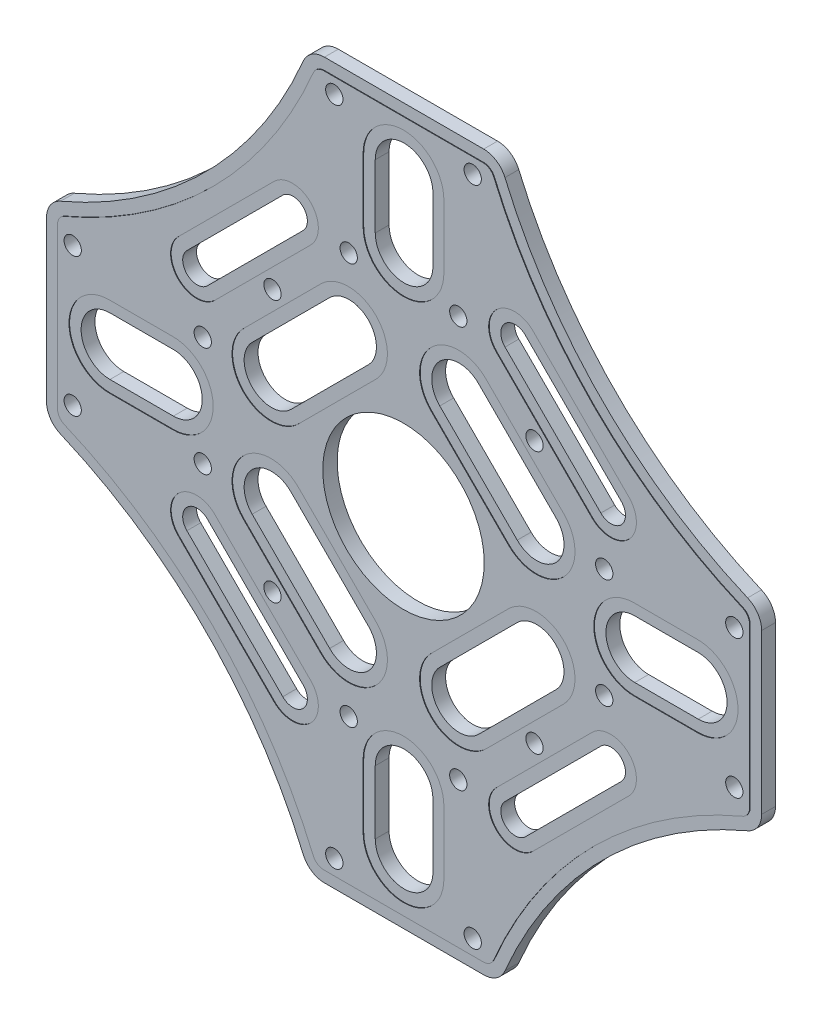
SolidWorks part; units mm, degrees
ref_plane "Alzado" through (0, 0, 0) normal (0, 0, 1) x (1, 0, 0)
ref_plane "Planta" through (0, 0, 0) normal (0, 1, 0) x (1, 0, 0)
ref_plane "Vista lateral" through (0, 0, 0) normal (1, 0, 0) x (0, 0, -1)
sketch "Croquis1" plane through (0, 0, 0) normal (0, 0, 1) x (1, 0, 0)
  line L0 (0, 62) -> (0, -62) construction
  line L1 (16.5, -62) -> (-16.5, -62)
  line L2 (16.5, -62) -> (16.5, -9.3094) construction
  line L3 (16.5, 62) -> (-16.5, 62)
  line L4 (-16.5, -62) -> (-16.5, -9.3094) construction
  line L5 (-62, 0) -> (62, 0) construction
  line L6 (0, 51) -> (0, 40) construction
  line L7 (62, -16.5) -> (9.3094, -16.5) construction
  line L8 (62, -16.5) -> (62, 16.5)
  line L9 (62, 16.5) -> (0, 16.5) construction
  line L10 (-62, -16.5) -> (-62, 16.5)
  line L11 (5, 51) -> (5, 40)
  line L12 (-5, 51) -> (-5, 40)
  line L13 (51, 0) -> (40, 0) construction
  line L14 (51, -5) -> (40, -5)
  line L15 (51, 5) -> (40, 5)
  line L16 (0, -51) -> (0, -40) construction
  line L17 (-5, -51) -> (-5, -40)
  line L18 (5, -51) -> (5, -40)
  line L19 (-51, 0) -> (-40, 0) construction
  line L20 (-51, 5) -> (-40, 5)
  line L21 (-51, -5) -> (-40, -5)
  line L22 (0, 0) -> (9.8995, -9.8995) construction
  line L23 (-35.8857, -19.2687) -> (-19.2687, -35.8857) construction
  line L24 (-34.1179, -17.5009) -> (-17.5009, -34.1179)
  line L25 (-37.6534, -21.0364) -> (-21.0364, -37.6534)
  line L26 (-22.981, -9.5459) -> (-9.5459, -22.981) construction
  line L27 (-19.6222, -6.1872) -> (-6.1872, -19.6222)
  line L28 (-26.3397, -12.9047) -> (-12.9047, -26.3397)
  line L29 (19.2687, -35.8857) -> (35.8857, -19.2687) construction
  line L30 (17.5009, -34.1179) -> (34.1179, -17.5009)
  line L31 (21.0364, -37.6534) -> (37.6534, -21.0364)
  line L32 (9.5459, -22.981) -> (22.981, -9.5459) construction
  line L33 (6.1872, -19.6222) -> (19.6222, -6.1872)
  line L34 (12.9047, -26.3397) -> (26.3397, -12.9047)
  line L35 (-19.2687, 35.8857) -> (-35.8857, 19.2687) construction
  line L36 (-17.5009, 34.1179) -> (-34.1179, 17.5009)
  line L37 (-21.0364, 37.6534) -> (-37.6534, 21.0364)
  line L38 (-9.5459, 22.981) -> (-22.981, 9.5459) construction
  line L39 (-6.1872, 19.6222) -> (-19.6222, 6.1872)
  line L40 (-12.9047, 26.3397) -> (-26.3397, 12.9047)
  line L41 (35.8857, 19.2687) -> (19.2687, 35.8857) construction
  line L42 (34.1179, 17.5009) -> (17.5009, 34.1179)
  line L43 (37.6534, 21.0364) -> (21.0364, 37.6534)
  line L44 (22.981, 9.5459) -> (9.5459, 22.981) construction
  line L45 (19.6222, 6.1872) -> (6.1872, 19.6222)
  line L46 (26.3397, 12.9047) -> (12.9047, 26.3397)
  line L47 (-9.3094, 16.5) -> (-62, 16.5) construction
  line L48 (-16.5, 9.3094) -> (-16.5, 62) construction
  line L49 (-9.3094, -16.5) -> (-62, -16.5) construction
  line L50 (16.5, 0) -> (16.5, 62) construction
  line L51 (12.9047, -12.9047) -> (56.3792, -56.3792) construction
  line L52 (29.3449, -29.3449) -> (34.2947, -34.2947)
  circle A0 centre (0, 0) radius 14
  arc A1 (5, 51) -> (-5, 51) centre (0, 51) ccw
  arc A2 (-5, 40) -> (5, 40) centre (0, 40) ccw
  arc A3 (51, -5) -> (51, 5) centre (51, 0) ccw
  arc A4 (40, 5) -> (40, -5) centre (40, 0) ccw
  arc A5 (-5, -51) -> (5, -51) centre (0, -51) ccw
  arc A6 (5, -40) -> (-5, -40) centre (0, -40) ccw
  arc A7 (-51, 5) -> (-51, -5) centre (-51, 0) ccw
  arc A8 (-40, -5) -> (-40, 5) centre (-40, 0) ccw
  arc A9 (-34.1179, -17.5009) -> (-37.6534, -21.0364) centre (-35.8857, -19.2687) ccw
  arc A10 (-21.0364, -37.6534) -> (-17.5009, -34.1179) centre (-19.2687, -35.8857) ccw
  arc A11 (-19.6222, -6.1872) -> (-26.3397, -12.9047) centre (-22.981, -9.5459) ccw
  arc A12 (-12.9047, -26.3397) -> (-6.1872, -19.6222) centre (-9.5459, -22.981) ccw
  arc A13 (17.5009, -34.1179) -> (21.0364, -37.6534) centre (19.2687, -35.8857) ccw
  arc A14 (37.6534, -21.0364) -> (34.1179, -17.5009) centre (35.8857, -19.2687) ccw
  arc A15 (6.1872, -19.6222) -> (12.9047, -26.3397) centre (9.5459, -22.981) ccw
  arc A16 (26.3397, -12.9047) -> (19.6222, -6.1872) centre (22.981, -9.5459) ccw
  arc A17 (-17.5009, 34.1179) -> (-21.0364, 37.6534) centre (-19.2687, 35.8857) ccw
  arc A18 (-37.6534, 21.0364) -> (-34.1179, 17.5009) centre (-35.8857, 19.2687) ccw
  arc A19 (-6.1872, 19.6222) -> (-12.9047, 26.3397) centre (-9.5459, 22.981) ccw
  arc A20 (-26.3397, 12.9047) -> (-19.6222, 6.1872) centre (-22.981, 9.5459) ccw
  arc A21 (34.1179, 17.5009) -> (37.6534, 21.0364) centre (35.8857, 19.2687) ccw
  arc A22 (21.0364, 37.6534) -> (17.5009, 34.1179) centre (19.2687, 35.8857) ccw
  arc A23 (19.6222, 6.1872) -> (26.3397, 12.9047) centre (22.981, 9.5459) ccw
  arc A24 (12.9047, 26.3397) -> (6.1872, 19.6222) centre (9.5459, 22.981) ccw
  arc A25 (62, -16.5) -> (16.5, -62) centre (90.5636, -90.5636) ccw
  arc A26 (-16.5, -62) -> (-62, -16.5) centre (-90.5636, -90.5636) ccw
  arc A27 (-62, 16.5) -> (-16.5, 62) centre (-90.5636, 90.5636) ccw
  arc A28 (16.5, 62) -> (62, 16.5) centre (90.5636, 90.5636) ccw
  point P0 (0, 0)
  point P6 (0, 0)
  point P18 (0, 45.5)
  point P24 (0, 35)
  point P30 (45.5, 0)
  point P37 (0, -45.5)
  point P44 (-45.5, 0)
  point P49 (0, 0)
  point P53 (-27.5772, -27.5772)
  point P60 (-16.2635, -16.2635)
  point P64 (27.5772, -27.5772)
  point P71 (16.2635, -16.2635)
  point P81 (-27.5772, 27.5772)
  point P88 (-16.2635, 16.2635)
  point P95 (27.5772, 27.5772)
  point P102 (16.2635, 16.2635)
  point P107 (0, 0)
  point P130 (0, 0)
  dimension "D5" = 28
  dimension "D9" = 4
  dimension "D1" = 124
  dimension "D2" = 33
  dimension "D3" = 124
  dimension "D4" = 33
  dimension "D6" = 10.5
  dimension "D7" = 10
  dimension "D8" = 45.5
  dimension "D10" = 45
  dimension "D11" = 23
  dimension "D12" = 9.5
  dimension "D13" = 5
  dimension "D14" = 39
  dimension "D16" = 7
  dimension "D15" = 4
  dimension "D17" = 4
extrude "Saliente-Extruir1" add sketch "Croquis1" along normal mid plane 2.5
fillet "Redondeo1" radius 4 8 edges at (-62, 16.5, 0) (-62, -16.5, 0) (-16.5, -62, 0) (16.5, -62, 0) (62, -16.5, 0) (62, 16.5, 0) (-16.5, 62, 0) (16.5, 62, 0)
sketch "Croquis2" plane through (0, 0, 1.25) normal (0, 0, 1) x (1, 0, 0)
  line L0 (19.6222, 6.1872) -> (6.1872, 19.6222) construction
  line L1 (26.3397, 12.9047) -> (12.9047, 26.3397) construction
  line L2 (37.6534, 21.0364) -> (21.0364, 37.6534) construction
  line L3 (34.1179, 17.5009) -> (17.5009, 34.1179) construction
  line L4 (19.6222, 6.1872) -> (6.1872, 19.6222)
  line L5 (26.3397, 12.9047) -> (12.9047, 26.3397)
  line L6 (37.6534, 21.0364) -> (21.0364, 37.6534)
  line L7 (34.1179, 17.5009) -> (17.5009, 34.1179)
  line L8 (39.0676, 22.4506) -> (22.4506, 39.0676)
  line L9 (32.7037, 16.0867) -> (16.0867, 32.7037)
  line L10 (18.208, 4.773) -> (4.773, 18.208)
  line L11 (27.7539, 14.3189) -> (14.3189, 27.7539)
  line L12 (5, 51) -> (5, 40) construction
  line L13 (-5, 51) -> (-5, 40) construction
  line L14 (-6.1872, 19.6222) -> (-19.6222, 6.1872) construction
  line L15 (-12.9047, 26.3397) -> (-26.3397, 12.9047) construction
  line L16 (-17.5009, 34.1179) -> (-34.1179, 17.5009) construction
  line L17 (-21.0364, 37.6534) -> (-37.6534, 21.0364) construction
  line L18 (-51, 5) -> (-40, 5) construction
  line L19 (-51, -5) -> (-40, -5) construction
  line L20 (-19.6222, -6.1872) -> (-6.1872, -19.6222) construction
  line L21 (-26.3397, -12.9047) -> (-12.9047, -26.3397) construction
  line L22 (-34.1179, -17.5009) -> (-17.5009, -34.1179) construction
  line L23 (-37.6534, -21.0364) -> (-21.0364, -37.6534) construction
  line L24 (-5, -51) -> (-5, -40) construction
  line L25 (5, -51) -> (5, -40) construction
  line L26 (6.1872, -19.6222) -> (19.6222, -6.1872) construction
  line L27 (12.9047, -26.3397) -> (26.3397, -12.9047) construction
  line L28 (17.5009, -34.1179) -> (34.1179, -17.5009) construction
  line L29 (21.0364, -37.6534) -> (37.6534, -21.0364) construction
  line L30 (51, 5) -> (40, 5) construction
  line L31 (51, -5) -> (40, -5) construction
  line L32 (5, 51) -> (5, 40)
  line L33 (-5, 51) -> (-5, 40)
  line L34 (-6.1872, 19.6222) -> (-19.6222, 6.1872)
  line L35 (-12.9047, 26.3397) -> (-26.3397, 12.9047)
  line L36 (-17.5009, 34.1179) -> (-34.1179, 17.5009)
  line L37 (-21.0364, 37.6534) -> (-37.6534, 21.0364)
  line L38 (-51, 5) -> (-40, 5)
  line L39 (-51, -5) -> (-40, -5)
  line L40 (-19.6222, -6.1872) -> (-6.1872, -19.6222)
  line L41 (-26.3397, -12.9047) -> (-12.9047, -26.3397)
  line L42 (-34.1179, -17.5009) -> (-17.5009, -34.1179)
  line L43 (-37.6534, -21.0364) -> (-21.0364, -37.6534)
  line L44 (-5, -51) -> (-5, -40)
  line L45 (5, -51) -> (5, -40)
  line L46 (6.1872, -19.6222) -> (19.6222, -6.1872)
  line L47 (12.9047, -26.3397) -> (26.3397, -12.9047)
  line L48 (17.5009, -34.1179) -> (34.1179, -17.5009)
  line L49 (21.0364, -37.6534) -> (37.6534, -21.0364)
  line L50 (51, 5) -> (40, 5)
  line L51 (51, -5) -> (40, -5)
  line L52 (-14.3189, 27.7539) -> (-27.7539, 14.3189)
  line L53 (-4.773, 18.208) -> (-18.208, 4.773)
  line L54 (-16.0867, 32.7037) -> (-32.7037, 16.0867)
  line L55 (-22.4506, 39.0676) -> (-39.0676, 22.4506)
  line L56 (-7, 51) -> (-7, 40)
  line L57 (7, 51) -> (7, 40)
  line L58 (-18.208, -4.773) -> (-4.773, -18.208)
  line L59 (-27.7539, -14.3189) -> (-14.3189, -27.7539)
  line L60 (-51, -7) -> (-40, -7)
  line L61 (-51, 7) -> (-40, 7)
  line L62 (-39.0676, -22.4506) -> (-22.4506, -39.0676)
  line L63 (-32.7037, -16.0867) -> (-16.0867, -32.7037)
  line L64 (-7, -51) -> (-7, -40)
  line L65 (7, -51) -> (7, -40)
  line L66 (14.3189, -27.7539) -> (27.7539, -14.3189)
  line L67 (4.773, -18.208) -> (18.208, -4.773)
  line L68 (16.0867, -32.7037) -> (32.7037, -16.0867)
  line L69 (22.4506, -39.0676) -> (39.0676, -22.4506)
  line L70 (51, -7) -> (40, -7)
  line L71 (51, 7) -> (40, 7)
  arc A0 (12.9047, 26.3397) -> (6.1872, 19.6222) centre (9.5459, 22.981) ccw construction
  arc A1 (19.6222, 6.1872) -> (26.3397, 12.9047) centre (22.981, 9.5459) ccw construction
  arc A2 (21.0364, 37.6534) -> (17.5009, 34.1179) centre (19.2687, 35.8857) ccw construction
  arc A3 (34.1179, 17.5009) -> (37.6534, 21.0364) centre (35.8857, 19.2687) ccw construction
  arc A4 (12.9047, 26.3397) -> (6.1872, 19.6222) centre (9.5459, 22.981) ccw
  arc A5 (19.6222, 6.1872) -> (26.3397, 12.9047) centre (22.981, 9.5459) ccw
  arc A6 (21.0364, 37.6534) -> (17.5009, 34.1179) centre (19.2687, 35.8857) ccw
  arc A7 (34.1179, 17.5009) -> (37.6534, 21.0364) centre (35.8857, 19.2687) ccw
  arc A8 (22.4506, 39.0676) -> (16.0867, 32.7037) centre (19.2687, 35.8857) ccw
  arc A9 (32.7037, 16.0867) -> (39.0676, 22.4506) centre (35.8857, 19.2687) ccw
  arc A10 (14.3189, 27.7539) -> (4.773, 18.208) centre (9.5459, 22.981) ccw
  arc A11 (18.208, 4.773) -> (27.7539, 14.3189) centre (22.981, 9.5459) ccw
  arc A12 (5, 51) -> (-5, 51) centre (0, 51) ccw construction
  arc A13 (-5, 40) -> (5, 40) centre (0, 40) ccw construction
  arc A14 (-26.3397, 12.9047) -> (-19.6222, 6.1872) centre (-22.981, 9.5459) ccw construction
  arc A15 (-6.1872, 19.6222) -> (-12.9047, 26.3397) centre (-9.5459, 22.981) ccw construction
  arc A16 (-17.5009, 34.1179) -> (-21.0364, 37.6534) centre (-19.2687, 35.8857) ccw construction
  arc A17 (-37.6534, 21.0364) -> (-34.1179, 17.5009) centre (-35.8857, 19.2687) ccw construction
  arc A18 (-40, -5) -> (-40, 5) centre (-40, 0) ccw construction
  arc A19 (-51, 5) -> (-51, -5) centre (-51, 0) ccw construction
  arc A20 (-34.1179, -17.5009) -> (-37.6534, -21.0364) centre (-35.8857, -19.2687) ccw construction
  arc A21 (-19.6222, -6.1872) -> (-26.3397, -12.9047) centre (-22.981, -9.5459) ccw construction
  arc A22 (-21.0364, -37.6534) -> (-17.5009, -34.1179) centre (-19.2687, -35.8857) ccw construction
  arc A23 (-12.9047, -26.3397) -> (-6.1872, -19.6222) centre (-9.5459, -22.981) ccw construction
  arc A24 (-5, -51) -> (5, -51) centre (0, -51) ccw construction
  arc A25 (5, -40) -> (-5, -40) centre (0, -40) ccw construction
  arc A26 (6.1872, -19.6222) -> (12.9047, -26.3397) centre (9.5459, -22.981) ccw construction
  arc A27 (26.3397, -12.9047) -> (19.6222, -6.1872) centre (22.981, -9.5459) ccw construction
  arc A28 (17.5009, -34.1179) -> (21.0364, -37.6534) centre (19.2687, -35.8857) ccw construction
  arc A29 (37.6534, -21.0364) -> (34.1179, -17.5009) centre (35.8857, -19.2687) ccw construction
  arc A30 (51, -5) -> (51, 5) centre (51, 0) ccw construction
  arc A31 (40, 5) -> (40, -5) centre (40, 0) ccw construction
  arc A32 (5, 51) -> (-5, 51) centre (0, 51) ccw
  arc A33 (-5, 40) -> (5, 40) centre (0, 40) ccw
  arc A34 (-26.3397, 12.9047) -> (-19.6222, 6.1872) centre (-22.981, 9.5459) ccw
  arc A35 (-6.1872, 19.6222) -> (-12.9047, 26.3397) centre (-9.5459, 22.981) ccw
  arc A36 (-17.5009, 34.1179) -> (-21.0364, 37.6534) centre (-19.2687, 35.8857) ccw
  arc A37 (-37.6534, 21.0364) -> (-34.1179, 17.5009) centre (-35.8857, 19.2687) ccw
  arc A38 (-40, -5) -> (-40, 5) centre (-40, 0) ccw
  arc A39 (-51, 5) -> (-51, -5) centre (-51, 0) ccw
  arc A40 (-34.1179, -17.5009) -> (-37.6534, -21.0364) centre (-35.8857, -19.2687) ccw
  arc A41 (-19.6222, -6.1872) -> (-26.3397, -12.9047) centre (-22.981, -9.5459) ccw
  arc A42 (-21.0364, -37.6534) -> (-17.5009, -34.1179) centre (-19.2687, -35.8857) ccw
  arc A43 (-12.9047, -26.3397) -> (-6.1872, -19.6222) centre (-9.5459, -22.981) ccw
  arc A44 (-5, -51) -> (5, -51) centre (0, -51) ccw
  arc A45 (5, -40) -> (-5, -40) centre (0, -40) ccw
  arc A46 (6.1872, -19.6222) -> (12.9047, -26.3397) centre (9.5459, -22.981) ccw
  arc A47 (26.3397, -12.9047) -> (19.6222, -6.1872) centre (22.981, -9.5459) ccw
  arc A48 (17.5009, -34.1179) -> (21.0364, -37.6534) centre (19.2687, -35.8857) ccw
  arc A49 (37.6534, -21.0364) -> (34.1179, -17.5009) centre (35.8857, -19.2687) ccw
  arc A50 (51, -5) -> (51, 5) centre (51, 0) ccw
  arc A51 (40, 5) -> (40, -5) centre (40, 0) ccw
  arc A52 (-4.773, 18.208) -> (-14.3189, 27.7539) centre (-9.5459, 22.981) ccw
  arc A53 (-27.7539, 14.3189) -> (-18.208, 4.773) centre (-22.981, 9.5459) ccw
  arc A54 (-39.0676, 22.4506) -> (-32.7037, 16.0867) centre (-35.8857, 19.2687) ccw
  arc A55 (-16.0867, 32.7037) -> (-22.4506, 39.0676) centre (-19.2687, 35.8857) ccw
  arc A56 (-7, 40) -> (7, 40) centre (0, 40) ccw
  arc A57 (7, 51) -> (-7, 51) centre (0, 51) ccw
  arc A58 (-14.3189, -27.7539) -> (-4.773, -18.208) centre (-9.5459, -22.981) ccw
  arc A59 (-18.208, -4.773) -> (-27.7539, -14.3189) centre (-22.981, -9.5459) ccw
  arc A60 (-40, -7) -> (-40, 7) centre (-40, 0) ccw
  arc A61 (-51, 7) -> (-51, -7) centre (-51, 0) ccw
  arc A62 (-22.4506, -39.0676) -> (-16.0867, -32.7037) centre (-19.2687, -35.8857) ccw
  arc A63 (-32.7037, -16.0867) -> (-39.0676, -22.4506) centre (-35.8857, -19.2687) ccw
  arc A64 (7, -40) -> (-7, -40) centre (0, -40) ccw
  arc A65 (-7, -51) -> (7, -51) centre (0, -51) ccw
  arc A66 (4.773, -18.208) -> (14.3189, -27.7539) centre (9.5459, -22.981) ccw
  arc A67 (27.7539, -14.3189) -> (18.208, -4.773) centre (22.981, -9.5459) ccw
  arc A68 (39.0676, -22.4506) -> (32.7037, -16.0867) centre (35.8857, -19.2687) ccw
  arc A69 (16.0867, -32.7037) -> (22.4506, -39.0676) centre (19.2687, -35.8857) ccw
  arc A70 (40, 7) -> (40, -7) centre (40, 0) ccw
  arc A71 (51, -7) -> (51, 7) centre (51, 0) ccw
  dimension "D1" = 2
  dimension "D2" = 2
extrude "Cortar-Extruir1" cut sketch "Croquis2" against normal blind 0.1
sketch "Croquis3" plane through (0, 0, 1.25) normal (0, 0, 1) x (1, 0, 0)
  line L0 (13.8045, 62) -> (-13.8045, 62) construction
  line L1 (-62, -13.8045) -> (-62, 13.8045) construction
  line L2 (13.8045, -62) -> (-13.8045, -62) construction
  line L3 (62, -13.8045) -> (62, 13.8045) construction
  line L4 (13.8045, 62) -> (-13.8045, 62)
  line L5 (-62, -13.8045) -> (-62, 13.8045)
  line L6 (13.8045, -62) -> (-13.8045, -62)
  line L7 (62, -13.8045) -> (62, 13.8045)
  line L8 (60, -13.8045) -> (60, 13.8045)
  line L9 (13.8045, -60) -> (-13.8045, -60)
  line L10 (-60, -13.8045) -> (-60, 13.8045)
  line L11 (13.8045, 60) -> (-13.8045, 60)
  arc A0 (-13.8045, 62) -> (-17.4869, 59.5622) centre (-13.8045, 58) ccw construction
  arc A1 (17.4869, 59.5622) -> (13.8045, 62) centre (13.8045, 58) ccw construction
  arc A2 (-59.5622, 17.4869) -> (-17.4869, 59.5622) centre (-90.5636, 90.5636) ccw construction
  arc A3 (-59.5622, 17.4869) -> (-62, 13.8045) centre (-58, 13.8045) ccw construction
  arc A4 (-62, -13.8045) -> (-59.5622, -17.4869) centre (-58, -13.8045) ccw construction
  arc A5 (-17.4869, -59.5622) -> (-59.5622, -17.4869) centre (-90.5636, -90.5636) ccw construction
  arc A6 (-17.4869, -59.5622) -> (-13.8045, -62) centre (-13.8045, -58) ccw construction
  arc A7 (13.8045, -62) -> (17.4869, -59.5622) centre (13.8045, -58) ccw construction
  arc A8 (59.5622, -17.4869) -> (17.4869, -59.5622) centre (90.5636, -90.5636) ccw construction
  arc A9 (59.5622, -17.4869) -> (62, -13.8045) centre (58, -13.8045) ccw construction
  arc A10 (17.4869, 59.5622) -> (59.5622, 17.4869) centre (90.5636, 90.5636) ccw construction
  arc A11 (62, 13.8045) -> (59.5622, 17.4869) centre (58, 13.8045) ccw construction
  arc A12 (-13.8045, 62) -> (-17.4869, 59.5622) centre (-13.8045, 58) ccw
  arc A13 (17.4869, 59.5622) -> (13.8045, 62) centre (13.8045, 58) ccw
  arc A14 (-59.5622, 17.4869) -> (-17.4869, 59.5622) centre (-90.5636, 90.5636) ccw
  arc A15 (-59.5622, 17.4869) -> (-62, 13.8045) centre (-58, 13.8045) ccw
  arc A16 (-62, -13.8045) -> (-59.5622, -17.4869) centre (-58, -13.8045) ccw
  arc A17 (-17.4869, -59.5622) -> (-59.5622, -17.4869) centre (-90.5636, -90.5636) ccw
  arc A18 (-17.4869, -59.5622) -> (-13.8045, -62) centre (-13.8045, -58) ccw
  arc A19 (13.8045, -62) -> (17.4869, -59.5622) centre (13.8045, -58) ccw
  arc A20 (59.5622, -17.4869) -> (17.4869, -59.5622) centre (90.5636, -90.5636) ccw
  arc A21 (59.5622, -17.4869) -> (62, -13.8045) centre (58, -13.8045) ccw
  arc A22 (17.4869, 59.5622) -> (59.5622, 17.4869) centre (90.5636, 90.5636) ccw
  arc A23 (62, 13.8045) -> (59.5622, 17.4869) centre (58, 13.8045) ccw
  arc A24 (15.6457, 58.7811) -> (58.7811, 15.6457) centre (90.5636, 90.5636) ccw
  arc A25 (60, 13.8045) -> (58.7811, 15.6457) centre (58, 13.8045) ccw
  arc A26 (58.7811, -15.6457) -> (60, -13.8045) centre (58, -13.8045) ccw
  arc A27 (58.7811, -15.6457) -> (15.6457, -58.7811) centre (90.5636, -90.5636) ccw
  arc A28 (13.8045, -60) -> (15.6457, -58.7811) centre (13.8045, -58) ccw
  arc A29 (-15.6457, -58.7811) -> (-13.8045, -60) centre (-13.8045, -58) ccw
  arc A30 (-15.6457, -58.7811) -> (-58.7811, -15.6457) centre (-90.5636, -90.5636) ccw
  arc A31 (-60, -13.8045) -> (-58.7811, -15.6457) centre (-58, -13.8045) ccw
  arc A32 (-58.7811, 15.6457) -> (-60, 13.8045) centre (-58, 13.8045) ccw
  arc A33 (-58.7811, 15.6457) -> (-15.6457, 58.7811) centre (-90.5636, 90.5636) ccw
  arc A34 (-13.8045, 60) -> (-15.6457, 58.7811) centre (-13.8045, 58) ccw
  arc A35 (15.6457, 58.7811) -> (13.8045, 60) centre (13.8045, 58) ccw
  dimension "D1" = 2
extrude "Cortar-Extruir2" cut sketch "Croquis3" against normal blind 0.1
sketch "Croquis4" plane through (0, 0, 1.25) normal (0, 0, 1) x (1, 0, 0)
  line L0 (56, 0) -> (35, 0) construction
  line L2 (33.642, -12) -> (57.358, -12) construction
  line L3 (33.642, -12) -> (33.642, 12) construction
  line L4 (33.642, 12) -> (57.358, 12) construction
  line L5 (57.358, -12) -> (57.358, 12) construction
  line L6 (33.642, -12) -> (57.358, 12) construction
  line L7 (33.642, 12) -> (57.358, -12) construction
  line L8 (56.1921, 9.5) -> (34.8079, 9.5) construction
  line L9 (56.1921, 9.5) -> (56.1921, -9.5) construction
  line L10 (56.1921, -9.5) -> (34.8079, -9.5) construction
  line L11 (34.8079, 9.5) -> (34.8079, -9.5) construction
  line L12 (56.1921, 9.5) -> (34.8079, -9.5) construction
  line L13 (56.1921, -9.5) -> (34.8079, 9.5) construction
  arc A0 (51, -5) -> (51, 5) centre (51, 0) ccw construction
  arc A1 (40, 5) -> (40, -5) centre (40, 0) ccw construction
  circle A2 centre (57.358, 12) radius 1.5
  circle A3 centre (57.358, -12) radius 1.5
  circle A4 centre (34.8079, 9.5) radius 1.5
  circle A5 centre (34.8079, -9.5) radius 1.5
  circle A6 centre (12, -57.358) radius 1.5
  circle A7 centre (-12, -57.358) radius 1.5
  circle A8 centre (-9.5, -34.8079) radius 1.5
  circle A9 centre (9.5, -34.8079) radius 1.5
  circle A10 centre (-57.358, -12) radius 1.5
  circle A11 centre (-57.358, 12) radius 1.5
  circle A12 centre (-34.8079, 9.5) radius 1.5
  circle A13 centre (-34.8079, -9.5) radius 1.5
  circle A14 centre (-12, 57.358) radius 1.5
  circle A15 centre (12, 57.358) radius 1.5
  circle A16 centre (9.5, 34.8079) radius 1.5
  circle A17 centre (-9.5, 34.8079) radius 1.5
  point P8 (45.5, 0)
  point P15 (45.5, 0)
  point P49 (0, 0)
  dimension "D2" = 3
  dimension "D3" = 3
  dimension "D5" = 3
  dimension "D6" = 3
  dimension "D1" = 24
  dimension "D4" = 19
  dimension "D7" = 4
extrude "Cortar-Extruir3" cut sketch "Croquis4" against normal blind 10
sketch "Croquis5" plane through (0, 0, 1.25) normal (0, 0, 1) x (1, 0, 0)
  line L0 (-25.8094, 25.8094) -> (-19.6222, 19.6222) construction
  line L1 (-34.1179, 17.5009) -> (-17.5009, 34.1179) construction
  line L2 (-12.9047, 26.3397) -> (-26.3397, 12.9047) construction
  circle A0 centre (-22.7158, 22.7158) radius 1.5
  circle A1 centre (22.7158, 22.7158) radius 1.5
  circle A2 centre (22.7158, -22.7158) radius 1.5
  circle A3 centre (-22.7158, -22.7158) radius 1.5
  point P17 (0, 0)
  dimension "D1" = 3
  dimension "D2" = 4
extrude "Cortar-Extruir4" cut sketch "Croquis5" against normal blind 10
